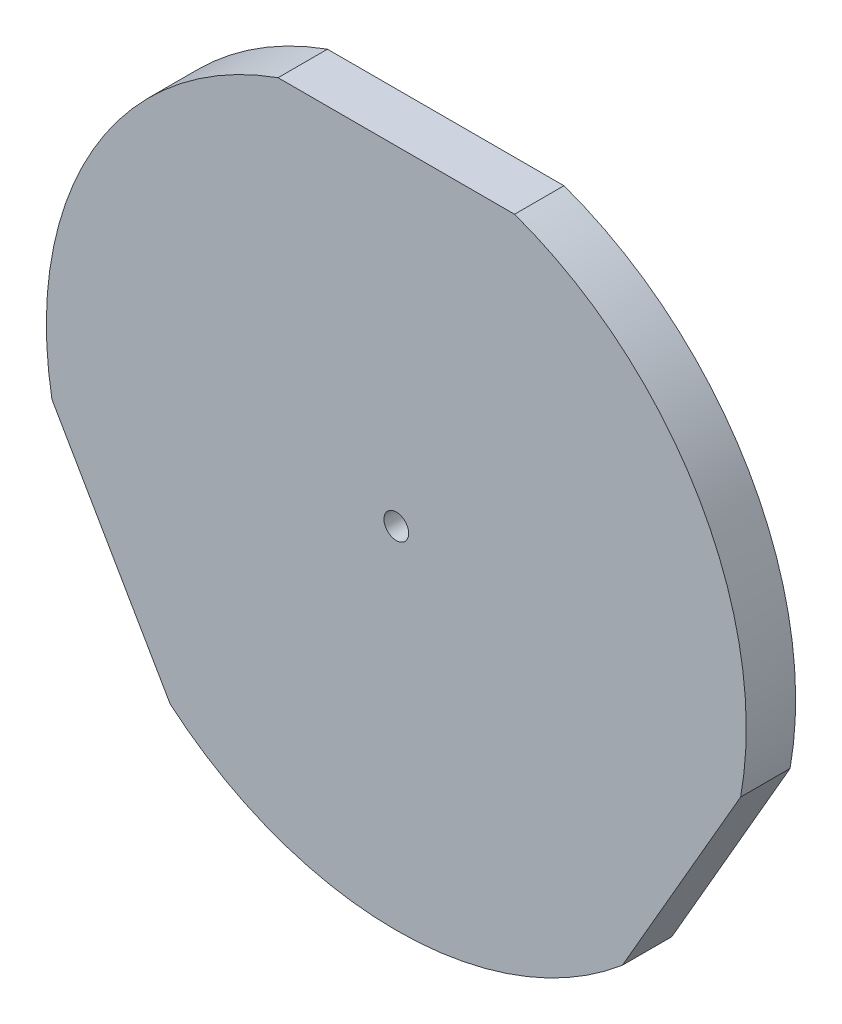
SolidWorks part; units mm, degrees
material "Pine"
ref_plane "Front Plane" through (0, 0, 0) normal (0, 0, 1) x (1, 0, 0)
ref_plane "Top Plane" through (0, 0, 0) normal (0, 1, 0) x (1, 0, 0)
ref_plane "Right Plane" through (0, 0, 0) normal (1, 0, 0) x (0, 0, -1)
sketch "Sketch1" plane through (0, 0, 0) normal (0, 0, 1) x (1, 0, 0)
  circle A0 centre (0, 0) radius 85
  circle A1 centre (0, 0) radius 3
  dimension "D1" = 170
  dimension "D2" = 6
extrude "Boss-Extrude1" add sketch "Sketch1" along normal blind 12
sketch "Sketch2" plane through (0, 0, 12) normal (0, 0, 1) x (1, 0, 0)
  line L0 (-28.7228, 80) -> (28.7228, 80)
  line L1 (0, 80) -> (0, 0) construction
  circle A0 centre (0, 0) radius 85 construction
  arc A1 (28.7228, 80) -> (-28.7228, 80) centre (0, 0) ccw
  dimension "D1" = 80
extrude "Cut-Extrude1" cut sketch "Sketch2" against normal up to next (12 mm away)
pattern_circular "CirPattern1" count 3 over 360 about axis through (0, 0, 0) along (0, 0, 1) of "Cut-Extrude1"
sketch "Sketch3" plane through (0, 0, 12) normal (0, 0, 1) x (1, 0, 0)
  line L0 (-74.282, -31.3397) -> (-64.282, -48.6603)
  line L1 (-54.9206, -64.8747) -> (-83.6434, -15.1253) construction
  line L2 (-64.282, -48.6603) -> (-81.6025, -58.6603)
  line L3 (-81.6025, -58.6603) -> (-91.6025, -41.3397)
  line L4 (-91.6025, -41.3397) -> (-74.282, -31.3397)
  line L5 (-86.6025, -50) -> (-69.282, -40) construction
  dimension "D1" = 20
  dimension "D2" = 20
extrude "Boss-Extrude2" [suppressed] add sketch "Sketch3" against normal blind 12
pattern_circular "CirPattern2" [suppressed] count 2 every 120
fillet "Fillet1" [suppressed] radius 5
